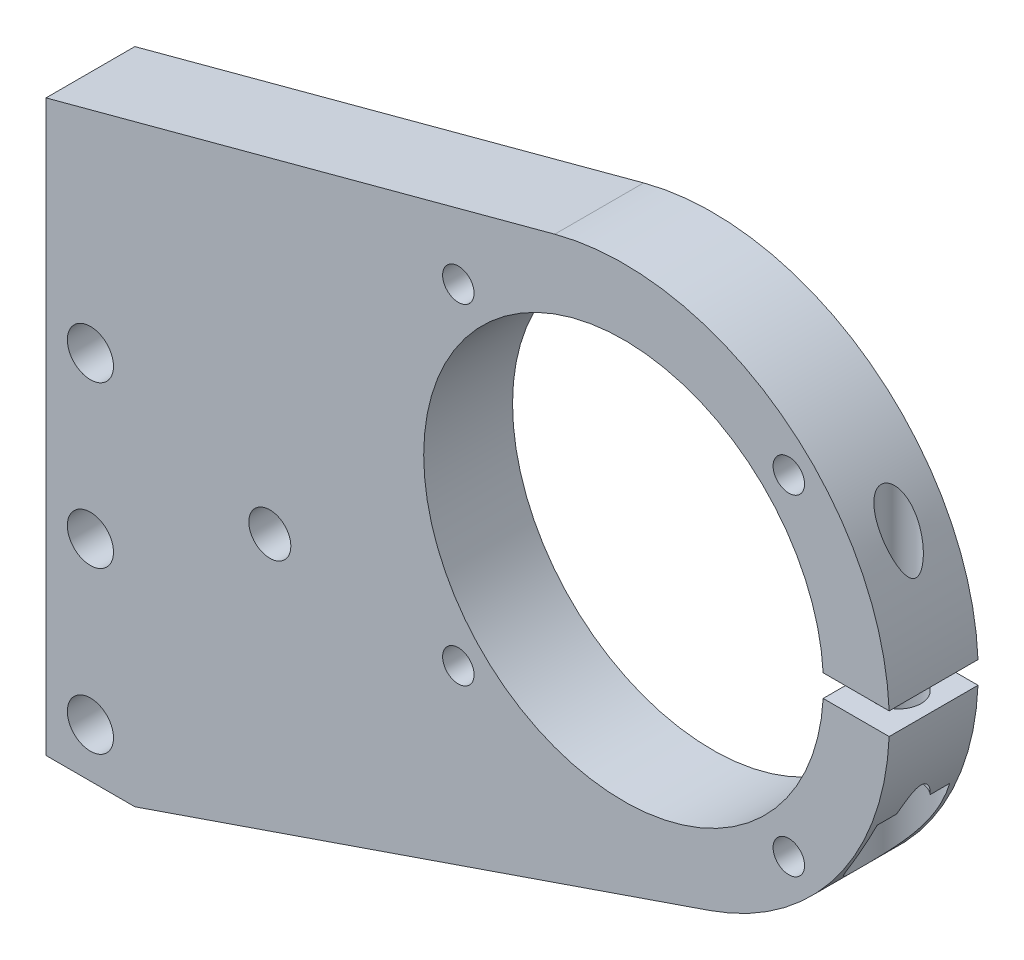
SolidWorks part; units mm, degrees
ref_plane "Front Plane" through (0, 0, 0) normal (0, 0, 1) x (1, 0, 0)
ref_plane "Top Plane" through (0, 0, 0) normal (0, 1, 0) x (1, 0, 0)
ref_plane "Right Plane" through (0, 0, 0) normal (1, 0, 0) x (0, 0, -1)
ref_plane "Plane1" through (0, 0, 0) normal (0, 0, -1) x (-1, 0, 0)
sketch "Sketch1" plane through (0, 0, 0) normal (0, 0, -1) x (-1, 0, 0)
  line L0 (224.1695, 127.7225) -> (151.4352, 147.2116)
  line L1 (129.2465, 74.5705) -> (211.4695, 46.305)
  line L2 (211.4695, 46.305) -> (224.1695, 46.305)
  line L3 (224.1695, 46.305) -> (224.1695, 127.7225)
  arc A0 (151.4352, 147.2116) -> (129.2465, 74.5705) centre (141.6001, 110.5064) ccw
extrude "Boss-Extrude1" add sketch "Sketch1" against normal blind 12.7
sketch "Sketch2" plane through (0, 0, 12.7) normal (0, 0, 1) x (1, 0, 0)
  line L0 (-103.6333, 112.0939) -> (-113.179, 112.0939)
  line L1 (-113.179, 108.9189) -> (-103.6333, 108.9189)
  arc A0 (-103.6333, 108.9189) -> (-103.6333, 112.0939) centre (-141.6001, 110.5064) ccw
  arc A1 (-113.179, 112.0939) -> (-113.179, 108.9189) centre (-141.6001, 110.5064) cw
extrude "Cut-Extrude1" cut sketch "Sketch2" against normal through all
ref_plane "Plane2" through (0, 110.5064, 0) normal (0, 1, 0) x (1, 0, 0)
sketch "Sketch3" plane through (0, 110.5064, 0) normal (0, 1, 0) x (1, 0, 0)
  line L0 (-113.0251, 0) -> (-141.6001, 0)
  line L1 (-141.6001, 0) -> (-141.6001, -12.7)
  line L2 (-141.6001, -12.7) -> (-113.0251, -12.7)
  line L3 (-113.0251, -12.7) -> (-113.0251, 0)
  line L4 (-141.6001, 0) -> (-141.6001, -12.7) construction
  dimension "D1" = 28.575
revolve "Cut-Revolve1" cut sketch "Sketch3" angle 360 about L4
hole_wizard "#8 Clearance Hole1" positions "Sketch5" profile "Sketch4" hole size "#8" standard "ANSI Inch"
sketch "Sketch5" plane through (0, 0, 12.7) normal (0, 0, 1) x (1, 0, 0)
  line L0 (-141.6001, 139.0814) -> (-141.6001, 81.9314) construction
  arc A0 (-113.0692, 112.0939) -> (-113.0692, 108.9189) centre (-141.6001, 110.5064) ccw construction
  point P0 (-117.9781, 86.8844)
  point P1 (-165.2221, 86.8844)
  point P2 (-165.2221, 134.1284)
  point P3 (-117.9781, 134.1284)
  point P12 (-141.6001, 110.5064)
  dimension "D1" = 47.244
  dimension "D2" = 47.244
  dimension "D3" = 23.622
  dimension "D4" = 47.244
  dimension "D5" = 23.622
  dimension "D6" = 23.622
  dimension "D7" = 47.244
  dimension "D8" = 23.622
sketch "Sketch4" plane through (-117.9781, 86.8844, 12.7) normal (1, 0, 0) x (0, -1, 0)
  line L0 (0, 0) -> (0, 12.7)
  line L1 (0, 12.7) -> (2.25, 12.7)
  line L2 (2.25, 12.7) -> (2.25, 0)
  line L5 (2.25, 0) -> (0, 0)
  line L11 (0, -6.35) -> (0, 107.95) construction
  dimension "Thru Hole Dia." = 4.5
  dimension "Thru Hole Depth" = 12.7
hole_wizard "1/4 Clearance Hole1" positions "Sketch7" profile "Sketch6" hole size "1/4" standard "ANSI Inch"
sketch "Sketch7" plane through (0, 0, 0) normal (0, 0, -1) x (-1, 0, 0)
  point P0 (217.8195, 53.305)
  point P1 (217.8195, 76.305)
  point P2 (217.8195, 99.305)
sketch "Sketch6" plane through (-217.8195, 53.305, 0) normal (1, 0, 0) x (0, 1, 0)
  line L0 (0, 0) -> (0, 12.7)
  line L1 (0, 12.7) -> (3.3, 12.7)
  line L2 (3.3, 12.7) -> (3.3, 0)
  line L5 (3.3, 0) -> (0, 0)
  line L11 (0, -6.35) -> (0, 107.95) construction
  dimension "Thru Hole Dia." = 6.6
  dimension "Thru Hole Depth" = 12.7
hole_wizard "#12 Clearance Hole1" positions "Sketch9" profile "Sketch8" hole size "#12" standard "ANSI Inch"
sketch "Sketch9" plane through (0, 0, 12.7) normal (0, 0, 1) x (1, 0, 0)
  point P0 (-192.1695, 89.7225)
sketch "Sketch8" plane through (-192.1695, 89.7225, 12.7) normal (1, 0, 0) x (0, -1, 0)
  line L0 (0, 0) -> (0, 12.7)
  line L1 (0, 12.7) -> (3, 12.7)
  line L2 (3, 12.7) -> (3, 0)
  line L5 (3, 0) -> (0, 0)
  line L11 (0, -6.35) -> (0, 107.95) construction
  dimension "Thru Hole Dia." = 6
  dimension "Thru Hole Depth" = 12.7
ref_plane "Plane3" through (0, 84.1425, 0) normal (0, -1, 0) x (-1, 0, 0)
hole_wizard "Hole1" positions "Sketch11" profile "Sketch10" legacy
sketch "Sketch11" plane through (0, 84.1425, 0) normal (0, -1, 0) x (-1, 0, 0)
  point P0 (108.6333, -6.35)
sketch "Sketch10" plane through (-108.6333, 84.1425, 6.35) normal (1, 0, 0) x (0, 0, -1)
  line L0 (0, 0) -> (0, 24.7764)
  line L1 (0, 24.7764) -> (3.2, 24.7764)
  line L2 (3.2, 24.7764) -> (3.2, 11.7764)
  line L3 (3.2, 11.7764) -> (5.6, 11.7764)
  line L4 (5.6, 11.7764) -> (5.6, 0)
  line L5 (5.6, 0) -> (0, 0)
  line L6 (0, 110) -> (0, -10) construction
  dimension "Diameter" = 6.4
  dimension "Depth" = 24.7764
  dimension "C-Bore Diameter" = 11.2
  dimension "C-Bore Depth" = 11.7764
hole_wizard "#10 Clearance Hole1" positions "Sketch13" profile "Sketch12" hole size "#10" standard "ANSI Inch"
sketch "Sketch13" plane through (0, 112.0939, 0) normal (0, -1, 0) x (-1, 0, 0)
  point P0 (108.6333, -6.35)
sketch "Sketch12" plane through (-108.6333, 112.0939, 6.35) normal (1, 0, 0) x (0, 0, -1)
  line L0 (0, 0) -> (0, 36.4125)
  line L1 (0, 36.4125) -> (2.5, 36.4125)
  line L2 (2.5, 36.4125) -> (2.5, 0)
  line L5 (2.5, 0) -> (0, 0)
  line L11 (0, -6.35) -> (0, 107.95) construction
  dimension "Thru Hole Dia." = 5
  dimension "Thru Hole Depth" = 36.4125
chamfer "Chamfer1" distance 3 angle 45 3 edges at (-221.1195, 53.305, 0) (-221.1195, 76.305, 0) (-221.1195, 99.305, 0)
sketch "Sketch14" plane through (0, 0, 0) normal (0, 0, -1) x (-1, 0, 0)
  circle A0 centre (192.1695, 89.7225) radius 4
  circle A1 centre (192.1695, 89.7225) radius 3 construction
  circle A2 centre (192.1695, 89.7225) radius 3
  point P0 (192.1695, 89.7225)
  dimension "D1" = 8
extrude "Boss-Extrude2" add sketch "Sketch14" against normal up to surface (12.7 mm away) up to face at (-189.1695, 89.7225, 12.7)
